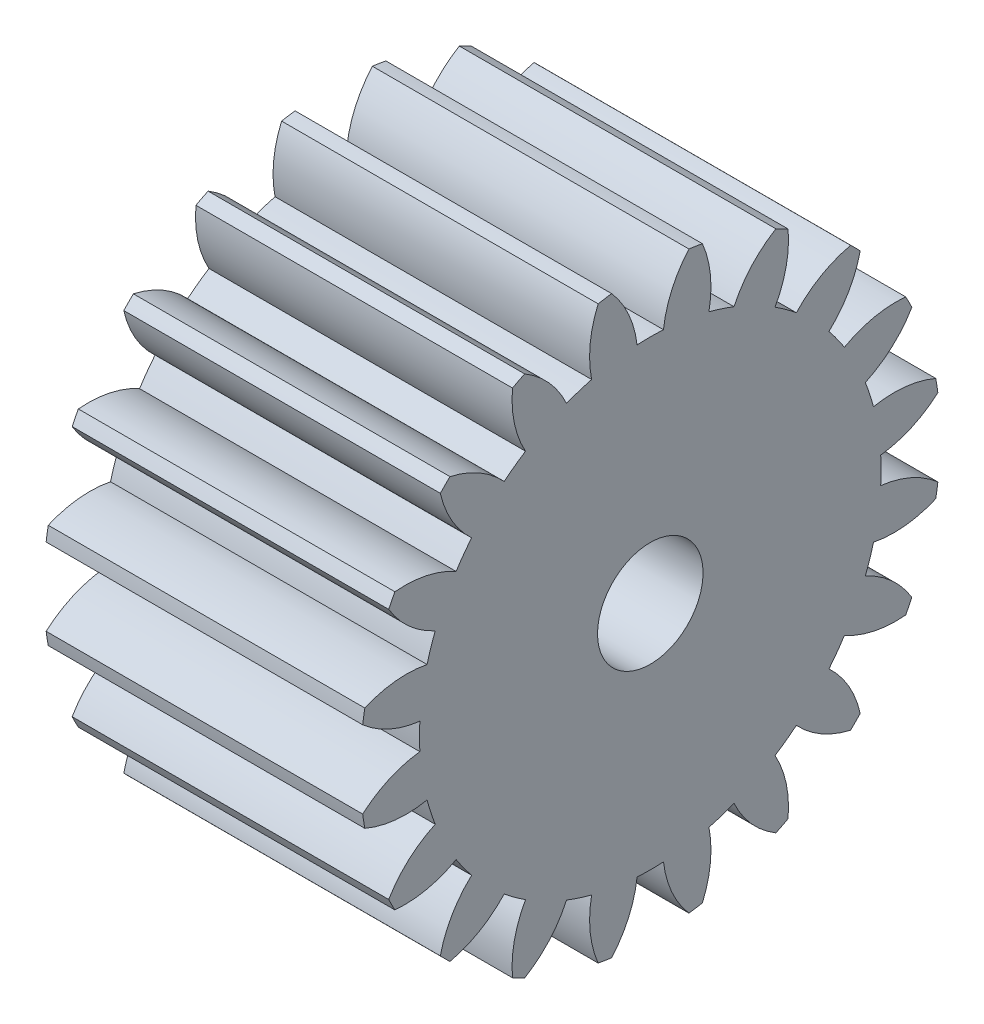
SolidWorks part; units mm, degrees
ref_plane "Plane1" through (0, 0, 0) normal (0, 0, 1) x (1, 0, 0)
ref_plane "Plane2" through (0, 0, 0) normal (0, 1, 0) x (1, 0, 0)
ref_plane "Plane3" through (0, 0, 0) normal (1, 0, 0) x (0, 0, -1)
sketch "HoldingSke" plane through (0, 0, 0) normal (0, 1, 0) x (1, 0, 0)
  line L0 (0, 0) -> (0.9397, -0.342)
  line L1 (-15, 0) -> (100, 0) construction
  line L2 (0, 0) -> (-2.1039, 2.3779)
  line L3 (0, 0) -> (-11.863, 4.5341)
  line L4 (0, 0) -> (8.1152, 2.9537)
  line L5 (0, 0) -> (-46.8476, -17.4728)
  line L6 (0, 0) -> (-9.9476, -6.7116)
  line L7 (-2.1039, 2.3779) -> (8.6586, 51.2059)
  line L8 (-76.2, 54.61) -> (-75.5, 54.61)
  line L9 (-71.009, 38.7566) -> (-53.1078, 45.2721)
  line L10 (-76.2, 71.12) -> (104.1128, 71.12)
  line L11 (0, 0) -> (-12, 0)
  line L12 (-76.2, 101.6) -> (-76.162, 101.6)
  line L13 (24.9733, 27.94) -> (52.9518, 28.4284)
  line L14 (24.9733, 27.94) -> (24.9743, 27.94)
  line L15 (24.9733, 27.94) -> (100.4006, 29.5858)
  line L16 (-63.627, -1) -> (-12.827, -1)
  circle A0 centre (0, 0) radius 2
  circle A1 centre (0, 0) radius 8.749
  circle A2 centre (0, 0) radius 37.5
  circle A3 centre (0, 0) radius 2
  dimension "MHD" = 17.498
  dimension "Hub_dia" = 75
  dimension "Bore" = 4
  dimension "MBD" = 4
  dimension "Num_teeth" = 20
  dimension "Pitch" = 1
  dimension "Overall_len" = 50
  dimension "Show_teeth" = 20
  dimension "Thickness" = 12
  dimension "OAL" = 50.0001
  dimension "T_dim" = 0.7
  dimension "Ap" = 20
  dimension "H" = 19.05
  dimension "Pitch_radius" = 180.3128
  dimension "Width" = 12
  dimension "Backlash" = 0.038
  dimension "Addendum_fac" = 1
  dimension "Dedendum_fac" = 1.25
  dimension "Clearance_fac" = 0.25
  dimension "Dedendum_add" = 0.001
  dimension "Module" = 1
sketch "BasProSke" plane through (0, 0, 0) normal (0, 1, 0) x (1, 0, 0)
  line L0 (-10, 0) -> (60, 0) construction
  line L1 (0, 0) -> (0, 11)
  line L2 (0, 0) -> (12, 0)
  line L3 (12, 0) -> (12, 11)
  line L4 (12, 11) -> (0, 11)
  dimension "Thickness" = 12
  dimension "Diameter" = 22
revolve "Base-Revolve" add sketch "BasProSke" angle 360 about L0
sketch "TooCutSke" plane through (0, 0, 0) normal (1, 0, 0) x (0, 0, -1)
  line L1 (0, 0) -> (0, 107) construction
  line L2 (0, 0) -> (-0.8511, 9.9637) construction
  line L3 (0, 0) -> (-3.1206, 19.7028) construction
  line L4 (-0.8511, 9.9637) -> (-1.5603, 9.8514) construction
  arc A0 (0.4999, 8.7347) -> (-0.4999, 8.7347) centre (0, 0) ccw
  arc A1 (1.4852, 10.9249) -> (-1.4852, 10.9249) centre (0, 0) ccw
  circle A2 centre (0, 0) radius 10 construction
  circle A3 centre (0, 0) radius 9.3969 construction
  arc A4 (-0.4999, 8.7347) -> (-1.4852, 10.9249) centre (-4.4722, 8.2645) ccw
  arc A5 (1.4852, 10.9249) -> (0.4999, 8.7347) centre (4.4722, 8.2645) ccw
  dimension "Root_dia" = 17.498
  dimension "Overcut_dia" = 22.0508
  dimension "Pitch_dia" = 20
  dimension "Base_dia" = 18.7939
  dimension "Flank_rad" = 4
  dimension "Half_ang" = 9
  dimension "Half_CT" = 0.7181
extrude "ToothCut" cut sketch "TooCutSke" along normal through all
fillet "Breaks" [suppressed] radius 0.02
fillet "RootFillets" [suppressed] radius 0.251
pattern_circular "TeethCuts" count 20 every 18 about axis through (-10, 0, 0) along (1, 0, 0) of "ToothCut", "RootFillets", "Breaks"
sketch "HubNeaOneSke" plane through (0, 0, 0) normal (-1, 0, 0) x (0, 0, 1)
  circle A0 centre (0, 0) radius 8.749
  dimension "Diameter" = 17.498
extrude "HubNearOne" [suppressed] add sketch "HubNeaOneSke" along normal blind 38.0001
sketch "HubNeaBotSke" plane through (0, 0, 0) normal (-1, 0, 0) x (0, 0, 1)
  circle A0 centre (0, 0) radius 8.749
  dimension "Diameter" = 17.498
extrude "HubNearBoth" [suppressed] add sketch "HubNeaBotSke" along normal blind 19
ref_plane "FarPln" through (12, 0, 0) normal (1, 0, 0) x (0, 0, -1)
sketch "HubFarSke" plane through (12, 0, 0) normal (1, 0, 0) x (0, 0, -1)
  circle A0 centre (0, 0) radius 8.749
  dimension "Diameter" = 17.498
extrude "HubFar" [suppressed] add sketch "HubFarSke" along normal blind 19
sketch "BorSke" plane through (0, 0, 0) normal (1, 0, 0) x (0, 0, -1)
  circle A0 centre (0, 0) radius 2
  dimension "Diameter" = 4
extrude "Bore" cut sketch "BorSke" along normal mid plane 100.0001
sketch "KeySke" plane through (0, 0, 0) normal (1, 0, 0) x (0, 0, -1)
  line L0 (-0.8, 0) -> (-0.8, 2.7)
  line L1 (-0.8, 2.7) -> (0.8, 2.7)
  line L2 (0.8, 2.7) -> (0.8, 0)
  line L3 (0, 0) -> (0, 34) construction
  line L4 (-0.8, 0) -> (0.8, 0)
  dimension "Offset" = 2.7
  dimension "Width" = 1.6
extrude "Keyway" [suppressed] cut sketch "KeySke" along normal mid plane 100.0001
pattern_circular "Keyway2" [suppressed] count 2 every 90 about axis through (-10, 0, 0) along (1, 0, 0)
equation "' \"Module@HoldingSke\" = 6.35"
equation "' \"Num_teeth@HoldingSke\" = 12"
equation "' \"Ap@HoldingSke\" =  20"
equation "' \"Ap@HoldingSke\" = 20"
equation "' \"Width@HoldingSke\" = 0.5 * 25.4"
equation "' \"Hub_dia@HoldingSke\"= 1 * 25.4"
equation "' \"Hub_dia@HoldingSke\" = 1 * 25.4"
equation "' \"Overall_len@HoldingSke\" = 1.0 * 25.4"
equation "' \"Bore@HoldingSke\" = 0.75 * 25.4"
equation "' \"T_dim@HoldingSke\" = 0.1 * 25.4"
equation "' \"Width@KeySke\" = 0.25 * 25.4"
equation "' \"Show_teeth@HoldingSke\" = 13"
equation "' \"Backlash@HoldingSke\" = 0.009 * 25.4"
equation "' \"Addendum_fac@HoldingSke\" = 1.0"
equation "' \"Dedendum_fac@HoldingSke\" = 1.25"
equation "' \"Dedendum_add@HoldingSke\" = 0.00005 * 25.4"
equation "' \"Clearance_fac@HoldingSke\" = 0.25"
equation "\"Pitch@HoldingSke\" = 1 / \"Module@HoldingSke\""
equation "\"Overcut_dia@TooCutSke\" = (\"Num_teeth@HoldingSke\" + 2 * \"Addendum_fac@HoldingSke\") / \"Pitch@HoldingSke\" + 0.002 * 25.4"
equation "\"Pitch_dia@TooCutSke\" = \"Num_teeth@HoldingSke\" / \"Pitch@HoldingSke\""
equation "\"Base_dia@TooCutSke\" = \"Num_teeth@HoldingSke\" / \"Pitch@HoldingSke\" * cos((\"Ap@HoldingSke\"  * 3.14159265 / 180))"
equation "\"Root_dia@TooCutSke\" = (\"Num_teeth@HoldingSke\" + 2) / \"Pitch@HoldingSke\" - 2 * (\"Addendum_fac@HoldingSke\" + \"Dedendum_fac@HoldingSke\") / \"Pitch@HoldingSke\" - \"Dedendum_add@HoldingSke\" * 2"
equation "\"Half_ang@TooCutSke\" = 180 / \"Num_teeth@HoldingSke\""
equation "\"Half_CT@TooCutSke\" = \"Num_teeth@HoldingSke\" / \"Pitch@HoldingSke\" * sin((3.14159265 / 2 / \"Num_teeth@HoldingSke\")) / 2 - 7 * \"Backlash@HoldingSke\" / 4"
equation "\"Flank_rad@TooCutSke\" = \"Num_teeth@HoldingSke\" / \"Pitch@HoldingSke\" / 5"
equation "\"Radius@RootFillets\" = \"Clearance_fac@HoldingSke\" / \"Pitch@HoldingSke\" + \"Dedendum_add@HoldingSke\""
equation "\"Break_rad@Breaks\" = 0.02 / \"Pitch@HoldingSke\""
equation "\"Thickness@HoldingSke\" = \"Width@HoldingSke\""
equation "\"OAL@HoldingSke\" = \"Thickness@HoldingSke\""
equation "\"MHD@HoldingSke\" = (\"Num_teeth@HoldingSke\" + 2) / \"Pitch@HoldingSke\" - 2 * (\"Addendum_fac@HoldingSke\" + \"Dedendum_fac@HoldingSke\")  / \"Pitch@HoldingSke\" - \"Dedendum_add@HoldingSke\" * 2"
equation "\"MBD@HoldingSke\" = (\"Num_teeth@HoldingSke\" + 2) / \"Pitch@HoldingSke\" - 2 * (\"Addendum_fac@HoldingSke\" + \"Dedendum_fac@HoldingSke\")  / \"Pitch@HoldingSke\" - \"Dedendum_add@HoldingSke\" * 2 - 0.002 * 25.4"
equation "\"MHD@HoldingSke\" = ((sgn( \"MHD@HoldingSke\" - \"Hub_dia@HoldingSke\" )-1)*( \"MHD@HoldingSke\" - \"Hub_dia@HoldingSke\" ))/-2+ \"Hub_dia@HoldingSke\""
equation "\"MBD@HoldingSke\" = ((sgn( \"MBD@HoldingSke\" - \"Bore@HoldingSke\" )-1)*( \"MBD@HoldingSke\" - \"Bore@HoldingSke\" ))/-2+ \"Bore@HoldingSke\""
equation "\"OAL@HoldingSke\" = ((sgn( \"OAL@HoldingSke\" - \"Overall_len@HoldingSke\" )+1)*( \"OAL@HoldingSke\" - \"Overall_len@HoldingSke\" ))/2 + \"Overall_len@HoldingSke\" + 0.000002 * 25.4"
equation "\"Num_teeth@TeethCuts\" = int( \"Show_teeth@HoldingSke\" ) + 1"
equation "\"Num_teeth@TeethCuts\" = ((sgn( \"Num_teeth@TeethCuts\" - \"Num_teeth@HoldingSke\" )-1)*( \"Num_teeth@TeethCuts\" - \"Num_teeth@HoldingSke\" ))/-2+ \"Num_teeth@HoldingSke\""
equation "\"Num_teeth@TeethCuts\" = ((sgn( \"Num_teeth@TeethCuts\" - 2.0)+1)*( \"Num_teeth@TeethCuts\" - 2.0))/2 +2.0"
equation "\"Angle@TeethCuts\" = 360.0 / \"Num_teeth@HoldingSke\""
equation "\"Diameter@BasProSke\" = (\"Num_teeth@HoldingSke\" + 2 * \"Addendum_fac@HoldingSke\") / \"Pitch@HoldingSke\""
equation "\"Thickness@BasProSke\"  = \"Thickness@HoldingSke\""
equation "' \"Fillet_rad@BasProSke\" =  \"Thickness@HoldingSke\" * 0.05"
equation "' \"Fillet_rad@BasProSke\" = \"Thickness@HoldingSke\" * 0.05"
equation "\"MHD@HoldingSke\" = ((sgn( \"MHD@HoldingSke\" - \"Root_dia@TooCutSke\" )-1)*( \"MHD@HoldingSke\" - \"Root_dia@TooCutSke\" ))/-2+ \"Root_dia@TooCutSke\""
equation "\"Diameter@HubNeaOneSke\" = \"MHD@HoldingSke\""
equation "\"Length@HubNearOne\" = \"OAL@HoldingSke\" - \"Thickness@BasProSke\""
equation "\"Diameter@HubNeaBotSke\" = \"MHD@HoldingSke\""
equation "\"Length@HubNearBoth\" = ( \"OAL@HoldingSke\" - \"Thickness@BasProSke\" ) / 2.0"
equation "\"Thickness@FarPln\" = \"Thickness@BasProSke\""
equation "\"Diameter@HubFarSke\" = \"MHD@HoldingSke\""
equation "\"Length@HubFar\" = ( \"OAL@HoldingSke\" - \"Thickness@BasProSke\" ) / 2.0"
equation "\"Diameter@BorSke\" = \"MBD@HoldingSke\""
equation "\"D1@Bore\" = \"OAL@HoldingSke\" * 2.0"
equation "\"D1@Keyway\" = \"OAL@HoldingSke\" * 2.0"
equation "\"Offset@KeySke\" = \"T_dim@HoldingSke\" + \"MBD@HoldingSke\" / 2.0"
